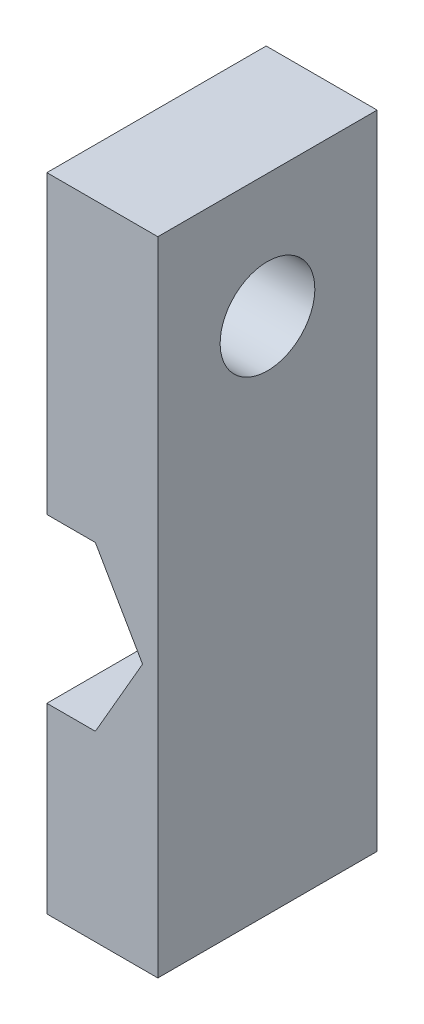
SolidWorks part; units mm, degrees
ref_plane "前基準面" through (0, 0, 0) normal (0, 0, 1) x (1, 0, 0)
ref_plane "上基準面" through (0, 0, 0) normal (0, 1, 0) x (1, 0, 0)
ref_plane "右基準面" through (0, 0, 0) normal (1, 0, 0) x (0, 0, -1)
sketch "草圖1" plane through (0, 0, 0) normal (0, 0, 1) x (1, 0, 0)
  line L0 (0.1325, -59.7793) -> (0.1325, -33.2793) construction
  line L1 (-10.8675, 4.6207) -> (11.1325, 4.6207)
  line L2 (-10.8675, 4.6207) -> (-10.8675, -59.7793)
  line L3 (-10.8675, -59.7793) -> (11.1325, -59.7793)
  line L4 (11.1325, 4.6207) -> (11.1325, -59.7793)
  line L5 (-6.9689, -29.1793) -> (7.2339, -37.3793) construction
  line L6 (9.6011, -33.2793) -> (4.8668, -25.0793)
  line L7 (4.8668, -25.0793) -> (-4.6017, -25.0793)
  line L8 (-4.6017, -25.0793) -> (-9.336, -33.2793)
  line L9 (-9.336, -33.2793) -> (-4.6017, -41.4793)
  line L10 (-4.6017, -41.4793) -> (4.8668, -41.4793)
  line L11 (4.8668, -41.4793) -> (9.6011, -33.2793)
  circle A0 centre (0.1325, -33.2793) radius 8.2 construction
  dimension "D1" = 22
  dimension "D2" = 64.4
  dimension "D3" = 26.5
  dimension "D4" = 16.4
extrude "填料-伸長1" add sketch "草圖1" along normal blind 22
sketch "草圖2" plane through (11.1325, 0, 0) normal (1, 0, 0) x (0, 0, -1)
  line L0 (-11, -59.7793) -> (-11, -7.7793) construction
  line L1 (-22, -59.7793) -> (0, -59.7793) construction
  circle A0 centre (-11, -7.7793) radius 4.75
  dimension "D2" = 9.5
  dimension "D1" = 52
extrude "除料-伸長1" cut sketch "草圖2" against normal blind 22
sketch "草圖3" plane through (0, 0, 0) normal (1, 0, 0) x (0, 0, -1)
  line L1 (0, 4.6207) -> (-22, 4.6207)
  line L2 (0, 4.6207) -> (0, -59.7793)
  line L3 (0, -59.7793) -> (-22, -59.7793)
  line L4 (-22, 4.6207) -> (-22, -59.7793)
extrude "除料-伸長2" cut sketch "草圖3" against normal blind 11
